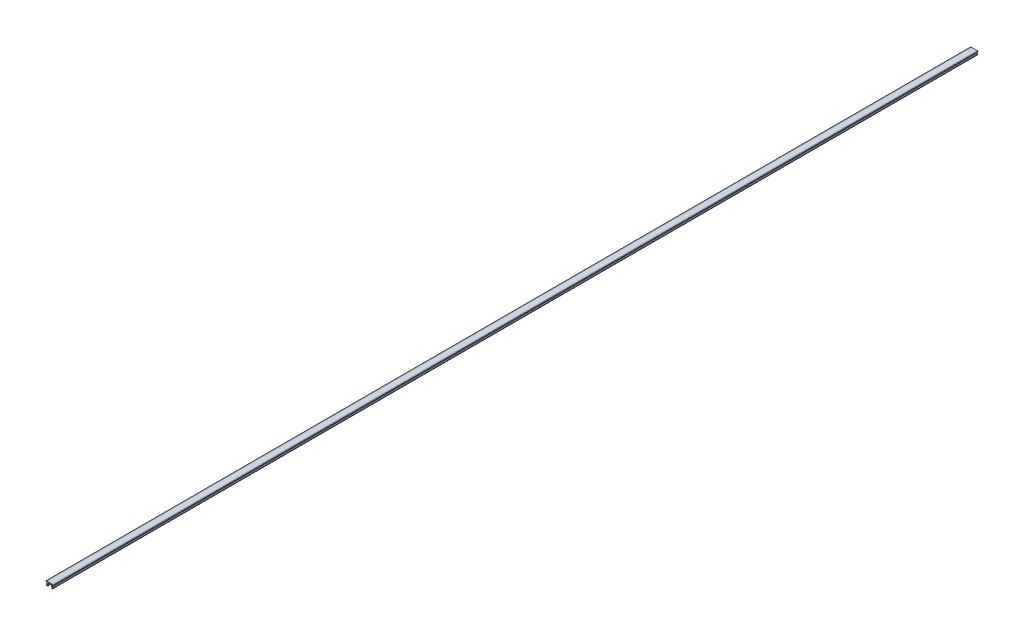
SolidWorks part; units mm, degrees
material "Пластик"
ref_plane "Спереди" through (0, 0, 0) normal (0, 0, 1) x (1, 0, 0)
ref_plane "Сверху" through (0, 0, 0) normal (0, 1, 0) x (1, 0, 0)
ref_plane "Справа" through (0, 0, 0) normal (1, 0, 0) x (0, 0, -1)
sketch "Эскиз1" plane through (0, 0, 0) normal (0, 0, 1) x (1, 0, 0)
  line L21 (-3.1, 0) -> (-4, -0.1587)
  line L22 (-4, -0.1587) -> (-4, -0.8)
  line L23 (-4, -0.8) -> (-3.1, -0.8)
  line L24 (-3.1, -0.8) -> (-3.1, -2.1962)
  line L25 (-3.1, -2.1962) -> (-3.6877, -3.2141)
  line L26 (-3.6877, -3.2141) -> (-3.1, -4.2321)
  line L27 (-2.1, -3.9641) -> (-2.533, -3.2141)
  line L28 (-2.533, -3.2141) -> (-2.1, -2.4641)
  line L29 (-2.1, -2.4641) -> (-2.1, -1)
  line L30 (-2.1, -1) -> (2.1, -1)
  line L31 (-3.1, 0) -> (3.1, 0)
  line L32 (0, 0) -> (0, -1) construction
  line L33 (2.1, -2.4641) -> (2.1, -1)
  line L34 (2.533, -3.2141) -> (2.1, -2.4641)
  line L35 (2.1, -3.9641) -> (2.533, -3.2141)
  line L36 (3.6877, -3.2141) -> (3.1, -4.2321)
  line L37 (3.1, -2.1962) -> (3.6877, -3.2141)
  line L38 (3.1, -0.8) -> (3.1, -2.1962)
  line L39 (4, -0.8) -> (3.1, -0.8)
  line L40 (4, -0.1587) -> (4, -0.8)
  line L41 (3.1, 0) -> (4, -0.1587)
  arc A0 (-3.1, -4.2321) -> (-2.1, -3.9641) centre (-2.6359, -3.9641) ccw
  arc A1 (3.1, -4.2321) -> (2.1, -3.9641) centre (2.6359, -3.9641) cw
  dimension "D1" = 8
  dimension "D2" = 6.2
  dimension "D3" = 4.5
  dimension "D4" = 150
  dimension "D5" = 120
  dimension "D6" = 1
  dimension "D7" = 1
  dimension "D8" = 1
  dimension "D9" = 0.8
  dimension "D10" = 1
  dimension "D11" = 10
  dimension "D12" = 1.5
extrude "Бобышка-Вытянуть1" add sketch "Эскиз1" along normal blind 1000
